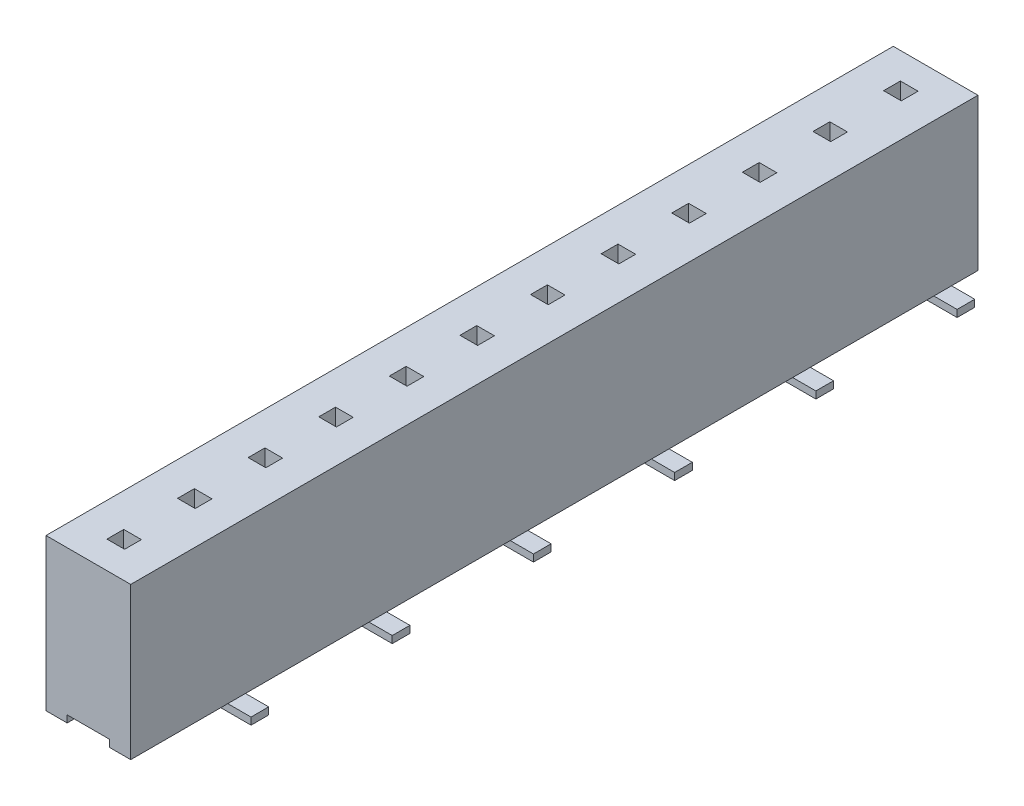
SolidWorks part; units mm, degrees
material "黄銅"
ref_plane "Front Plane" through (0, 0, 0) normal (0, 0, 1) x (1, 0, 0)
ref_plane "Top Plane" through (0, 0, 0) normal (0, 1, 0) x (1, 0, 0)
ref_plane "Right Plane" through (0, 0, 0) normal (1, 0, 0) x (0, 0, -1)
sketch "Sketch1" plane through (0, 0, 0) normal (0, 0, 1) x (1, 0, 0)
  line L1 (0, 0) -> (2.4, 0)
  line L2 (0, 0) -> (0, -4.3)
  line L3 (0, -4.3) -> (2.4, -4.3)
  line L4 (2.4, 0) -> (2.4, -4.3)
  dimension "D1" = 4.3
  dimension "D2" = 2.4
extrude "Boss-Extrude1" add sketch "Sketch1" against normal blind 24
sketch "Sketch2" plane through (0, 0, 0) normal (0, 0, 1) x (1, 0, 0)
  line L0 (0, -4.3) -> (2.4, -4.3) construction
  line L1 (0.6, -4.3) -> (1.8, -4.3)
  line L2 (0.6, -4.3) -> (0.6, -4.1)
  line L3 (0.6, -4.1) -> (1.8, -4.1)
  line L4 (1.8, -4.3) -> (1.8, -4.1)
  line L5 (0, 0) -> (0, -4.3) construction
  line L6 (2.4, -4.3) -> (2.4, 0) construction
  dimension "D1" = 0.6
  dimension "D2" = 0.6
  dimension "D3" = 0.2
extrude "Cut-Extrude1" cut sketch "Sketch2" against normal through all
sketch "Sketch3" plane through (0, -4.1, 0) normal (0, -1, 0) x (-1, 0, 0)
  line L1 (-0.9576, 0.75) -> (-1.4576, 0.75)
  line L2 (-0.9576, 0.75) -> (-0.9576, 1.25)
  line L3 (-0.9576, 1.25) -> (-1.4576, 1.25)
  line L4 (-1.4576, 0.75) -> (-1.4576, 1.25)
  line L6 (-0.9576, 2.75) -> (-1.4576, 2.75)
  line L8 (-1.4576, 2.75) -> (-1.4576, 3.25)
  line L9 (-0.9576, 2.75) -> (-0.9576, 3.25)
  line L10 (-0.9576, 3.25) -> (-1.4576, 3.25)
  line L11 (-0.9576, 4.75) -> (-1.4576, 4.75)
  line L12 (-1.4576, 4.75) -> (-1.4576, 5.25)
  line L13 (-0.9576, 4.75) -> (-0.9576, 5.25)
  line L14 (-0.9576, 5.25) -> (-1.4576, 5.25)
  line L15 (-0.9576, 6.75) -> (-1.4576, 6.75)
  line L16 (-1.4576, 6.75) -> (-1.4576, 7.25)
  line L17 (-0.9576, 6.75) -> (-0.9576, 7.25)
  line L18 (-0.9576, 7.25) -> (-1.4576, 7.25)
  line L19 (-0.9576, 8.75) -> (-1.4576, 8.75)
  line L20 (-1.4576, 8.75) -> (-1.4576, 9.25)
  line L21 (-0.9576, 8.75) -> (-0.9576, 9.25)
  line L22 (-0.9576, 9.25) -> (-1.4576, 9.25)
  line L23 (-0.9576, 10.75) -> (-1.4576, 10.75)
  line L24 (-1.4576, 10.75) -> (-1.4576, 11.25)
  line L25 (-0.9576, 10.75) -> (-0.9576, 11.25)
  line L26 (-0.9576, 11.25) -> (-1.4576, 11.25)
  line L27 (-0.9576, 12.75) -> (-1.4576, 12.75)
  line L28 (-1.4576, 12.75) -> (-1.4576, 13.25)
  line L29 (-0.9576, 12.75) -> (-0.9576, 13.25)
  line L30 (-0.9576, 13.25) -> (-1.4576, 13.25)
  line L31 (-0.9576, 14.75) -> (-1.4576, 14.75)
  line L32 (-1.4576, 14.75) -> (-1.4576, 15.25)
  line L33 (-0.9576, 14.75) -> (-0.9576, 15.25)
  line L34 (-0.9576, 15.25) -> (-1.4576, 15.25)
  line L35 (-0.9576, 16.75) -> (-1.4576, 16.75)
  line L36 (-1.4576, 16.75) -> (-1.4576, 17.25)
  line L37 (-0.9576, 16.75) -> (-0.9576, 17.25)
  line L38 (-0.9576, 17.25) -> (-1.4576, 17.25)
  line L39 (-0.9576, 18.75) -> (-1.4576, 18.75)
  line L40 (-1.4576, 18.75) -> (-1.4576, 19.25)
  line L41 (-0.9576, 18.75) -> (-0.9576, 19.25)
  line L42 (-0.9576, 19.25) -> (-1.4576, 19.25)
  line L43 (-0.9576, 20.75) -> (-1.4576, 20.75)
  line L44 (-1.4576, 20.75) -> (-1.4576, 21.25)
  line L45 (-0.9576, 20.75) -> (-0.9576, 21.25)
  line L46 (-0.9576, 21.25) -> (-1.4576, 21.25)
  line L47 (-0.9576, 22.75) -> (-1.4576, 22.75)
  line L48 (-1.4576, 22.75) -> (-1.4576, 23.25)
  line L49 (-0.9576, 22.75) -> (-0.9576, 23.25)
  line L50 (-0.9576, 23.25) -> (-1.4576, 23.25)
  dimension "D1" = 0.5
  dimension "D2" = 0.5
  dimension "D3" = 12
extrude "Boss-Extrude2" add sketch "Sketch3" along normal blind 0.4
sketch "Sketch7" plane through (0, 0, 0) normal (0, 1, 0) x (1, 0, 0)
  line L0 (0.9519, 20.7743) -> (1.4519, 20.7743)
  line L2 (1.4519, 21.25) -> (1.4519, 20.7743)
  line L3 (0.9519, 23.25) -> (1.4519, 23.25)
  line L4 (0.9519, 23.25) -> (0.9519, 22.7743)
  line L5 (0.9519, 22.7743) -> (1.4519, 22.7743)
  line L6 (1.4519, 23.25) -> (1.4519, 22.7743)
  line L7 (0.9519, 21.25) -> (1.4519, 21.25)
  line L8 (0.9519, 21.25) -> (0.9519, 20.7743)
  line L9 (0.9519, 18.7743) -> (1.4519, 18.7743)
  line L10 (1.4519, 19.25) -> (1.4519, 18.7743)
  line L11 (0.9519, 19.25) -> (1.4519, 19.25)
  line L12 (0.9519, 19.25) -> (0.9519, 18.7743)
  line L13 (0.9519, 16.7743) -> (1.4519, 16.7743)
  line L14 (1.4519, 17.25) -> (1.4519, 16.7743)
  line L15 (0.9519, 17.25) -> (1.4519, 17.25)
  line L16 (0.9519, 17.25) -> (0.9519, 16.7743)
  line L17 (0.9519, 14.7743) -> (1.4519, 14.7743)
  line L18 (1.4519, 15.25) -> (1.4519, 14.7743)
  line L19 (0.9519, 15.25) -> (1.4519, 15.25)
  line L20 (0.9519, 15.25) -> (0.9519, 14.7743)
  line L21 (0.9519, 12.7743) -> (1.4519, 12.7743)
  line L22 (1.4519, 13.25) -> (1.4519, 12.7743)
  line L23 (0.9519, 13.25) -> (1.4519, 13.25)
  line L24 (0.9519, 13.25) -> (0.9519, 12.7743)
  line L25 (0.9519, 10.7743) -> (1.4519, 10.7743)
  line L26 (1.4519, 11.25) -> (1.4519, 10.7743)
  line L27 (0.9519, 11.25) -> (1.4519, 11.25)
  line L28 (0.9519, 11.25) -> (0.9519, 10.7743)
  line L29 (0.9519, 8.7743) -> (1.4519, 8.7743)
  line L30 (1.4519, 9.25) -> (1.4519, 8.7743)
  line L31 (0.9519, 9.25) -> (1.4519, 9.25)
  line L32 (0.9519, 9.25) -> (0.9519, 8.7743)
  line L33 (0.9519, 6.7743) -> (1.4519, 6.7743)
  line L34 (1.4519, 7.25) -> (1.4519, 6.7743)
  line L35 (0.9519, 7.25) -> (1.4519, 7.25)
  line L36 (0.9519, 7.25) -> (0.9519, 6.7743)
  line L37 (0.9519, 4.7743) -> (1.4519, 4.7743)
  line L38 (1.4519, 5.25) -> (1.4519, 4.7743)
  line L39 (0.9519, 5.25) -> (1.4519, 5.25)
  line L40 (0.9519, 5.25) -> (0.9519, 4.7743)
  line L41 (0.9519, 2.7743) -> (1.4519, 2.7743)
  line L42 (1.4519, 3.25) -> (1.4519, 2.7743)
  line L43 (0.9519, 3.25) -> (1.4519, 3.25)
  line L44 (0.9519, 3.25) -> (0.9519, 2.7743)
  line L45 (0.9519, 0.7743) -> (1.4519, 0.7743)
  line L46 (1.4519, 1.25) -> (1.4519, 0.7743)
  line L47 (0.9519, 1.25) -> (1.4519, 1.25)
  line L48 (0.9519, 1.25) -> (0.9519, 0.7743)
  dimension "D1" = 0.5
  dimension "D2" = 12
extrude "Cut-Extrude2" cut sketch "Sketch7" against normal blind 3.5
sketch "Sketch8" plane through (0, -4.5, 0) normal (0, -1, 0) x (-1, 0, 0)
  line L0 (0.7574, 1) -> (-3.6964, 1) construction
  line L1 (1.5434, 23) -> (-3.3728, 23) construction
sketch "ｽｹｯﾁ1" plane through (1.4576, 0, 0) normal (1, 0, 0) x (0, 0, -1)
  line L0 (23.25, -4.5) -> (23.25, -4.1) construction
  line L1 (23.25, -4.3) -> (22.75, -4.3)
  line L2 (23.25, -4.3) -> (23.25, -4.5)
  line L3 (23.25, -4.5) -> (22.75, -4.5)
  line L4 (22.75, -4.3) -> (22.75, -4.5)
  line L5 (19.25, -4.5) -> (19.25, -4.1) construction
  line L6 (19.25, -4.3) -> (18.75, -4.3)
  line L7 (19.25, -4.3) -> (19.25, -4.5)
  line L8 (19.25, -4.5) -> (18.75, -4.5)
  line L9 (18.75, -4.3) -> (18.75, -4.5)
  line L10 (15.25, -4.5) -> (15.25, -4.1) construction
  line L11 (15.25, -4.3) -> (14.75, -4.3)
  line L12 (15.25, -4.3) -> (15.25, -4.5)
  line L13 (15.25, -4.5) -> (14.75, -4.5)
  line L14 (14.75, -4.3) -> (14.75, -4.5)
  line L15 (11.25, -4.5) -> (11.25, -4.1) construction
  line L16 (11.25, -4.3) -> (10.75, -4.3)
  line L17 (11.25, -4.3) -> (11.25, -4.5)
  line L18 (11.25, -4.5) -> (10.75, -4.5)
  line L19 (10.75, -4.3) -> (10.75, -4.5)
  line L20 (7.25, -4.5) -> (7.25, -4.1) construction
  line L21 (7.25, -4.3) -> (6.75, -4.3)
  line L22 (7.25, -4.3) -> (7.25, -4.5)
  line L23 (7.25, -4.5) -> (6.75, -4.5)
  line L24 (6.75, -4.3) -> (6.75, -4.5)
  line L25 (3.25, -4.5) -> (3.25, -4.1) construction
  line L26 (3.25, -4.3) -> (2.75, -4.3)
  line L27 (3.25, -4.3) -> (3.25, -4.5)
  line L28 (3.25, -4.5) -> (2.75, -4.5)
  line L29 (2.75, -4.3) -> (2.75, -4.5)
extrude "ﾎﾞｽ - 押し出し1" add sketch "ｽｹｯﾁ1" along normal blind 1.6
sketch "ｽｹｯﾁ2" plane through (0.9576, 0, 0) normal (-1, 0, 0) x (0, 0, 1)
  line L0 (-0.75, -4.5) -> (-0.75, -4.1) construction
  line L1 (-0.75, -4.3) -> (-1.25, -4.3)
  line L2 (-0.75, -4.3) -> (-0.75, -4.5)
  line L3 (-0.75, -4.5) -> (-1.25, -4.5)
  line L4 (-1.25, -4.3) -> (-1.25, -4.5)
  line L5 (-4.75, -4.5) -> (-4.75, -4.1) construction
  line L6 (-4.75, -4.3) -> (-5.25, -4.3)
  line L7 (-4.75, -4.3) -> (-4.75, -4.5)
  line L8 (-4.75, -4.5) -> (-5.25, -4.5)
  line L9 (-5.25, -4.3) -> (-5.25, -4.5)
  line L10 (-8.75, -4.5) -> (-8.75, -4.1) construction
  line L11 (-8.75, -4.3) -> (-9.25, -4.3)
  line L12 (-8.75, -4.3) -> (-8.75, -4.5)
  line L13 (-8.75, -4.5) -> (-9.25, -4.5)
  line L14 (-9.25, -4.3) -> (-9.25, -4.5)
  line L15 (-12.75, -4.5) -> (-12.75, -4.1) construction
  line L16 (-12.75, -4.3) -> (-13.25, -4.3)
  line L17 (-12.75, -4.3) -> (-12.75, -4.5)
  line L18 (-12.75, -4.5) -> (-13.25, -4.5)
  line L19 (-13.25, -4.3) -> (-13.25, -4.5)
  line L20 (-16.75, -4.5) -> (-16.75, -4.1) construction
  line L21 (-16.75, -4.3) -> (-17.25, -4.3)
  line L22 (-16.75, -4.3) -> (-16.75, -4.5)
  line L23 (-16.75, -4.5) -> (-17.25, -4.5)
  line L24 (-17.25, -4.3) -> (-17.25, -4.5)
  line L25 (-20.75, -4.5) -> (-20.75, -4.1) construction
  line L26 (-20.75, -4.3) -> (-21.25, -4.3)
  line L27 (-20.75, -4.3) -> (-20.75, -4.5)
  line L28 (-20.75, -4.5) -> (-21.25, -4.5)
  line L29 (-21.25, -4.3) -> (-21.25, -4.5)
extrude "ﾎﾞｽ - 押し出し2" add sketch "ｽｹｯﾁ2" along normal blind 1.6 separate body
